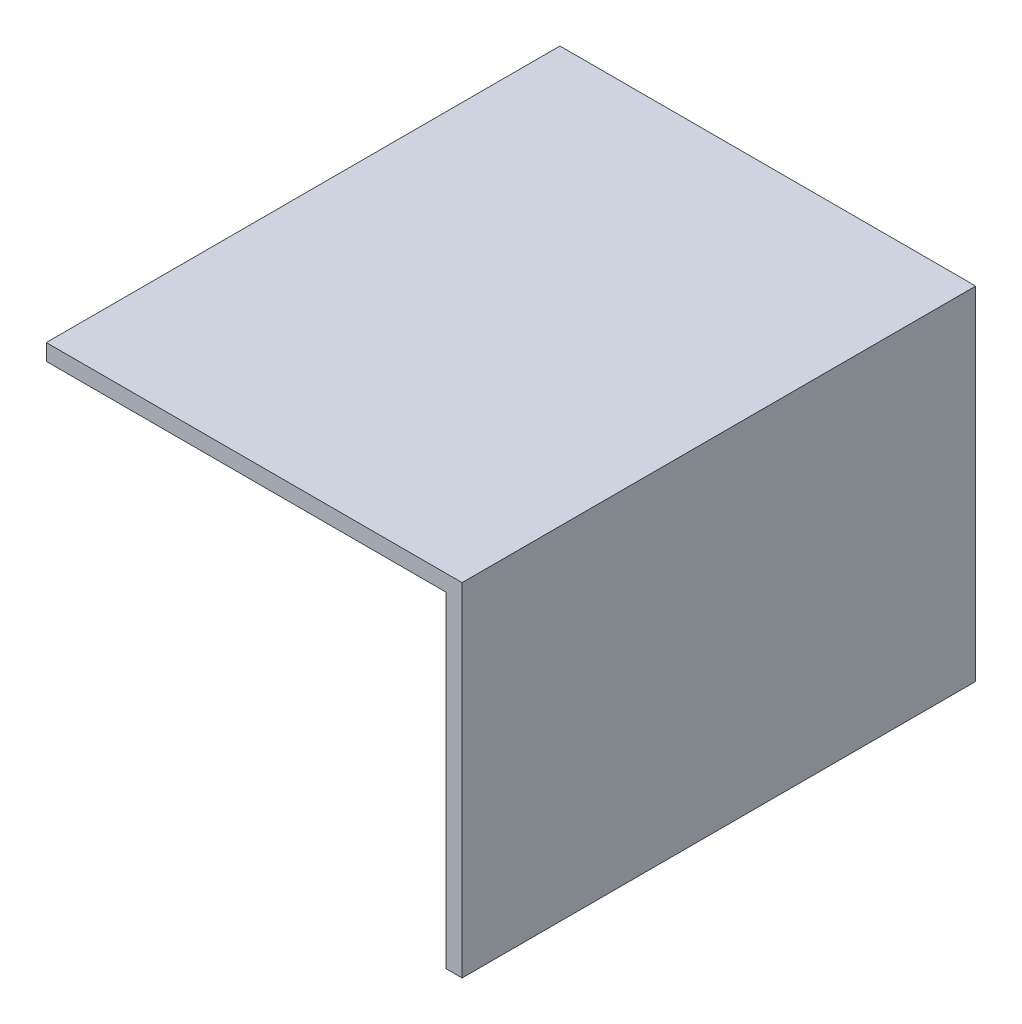
SolidWorks part; units mm, degrees
ref_plane "Front Plane" through (0, 0, 0) normal (0, 0, 1) x (1, 0, 0)
ref_plane "Top Plane" through (0, 0, 0) normal (0, 1, 0) x (1, 0, 0)
ref_plane "Right Plane" through (0, 0, 0) normal (1, 0, 0) x (0, 0, -1)
sketch "Sketch1" plane through (0, 0, 0) normal (0, 1, 0) x (1, 0, 0)
  line L1 (-25.5, -31.5) -> (25.5, -31.5)
  line L2 (-25.5, -31.5) -> (-25.5, 31.5)
  line L3 (-25.5, 31.5) -> (25.5, 31.5)
  line L4 (25.5, -31.5) -> (25.5, 31.5)
  line L5 (-25.5, -31.5) -> (25.5, 31.5) construction
  line L6 (-25.5, 31.5) -> (25.5, -31.5) construction
  point P0 (0, 0)
extrude "Boss-Extrude1" add sketch "Sketch1" along normal blind 42
sketch "Sketch3" plane through (0, 0, 0) normal (0, -1, 0) x (-1, 0, 0)
  line L0 (25.5, -31.5) -> (-25.5, -31.5) construction
  line L1 (25.5, 31.5) -> (-23.5, 31.5)
  line L2 (25.5, 31.5) -> (25.5, -31.5)
  line L3 (25.5, -31.5) -> (-23.5, -31.5)
  line L4 (-23.5, 31.5) -> (-23.5, -31.5)
extrude "Cut-Extrude2" cut sketch "Sketch3" against normal blind 40
